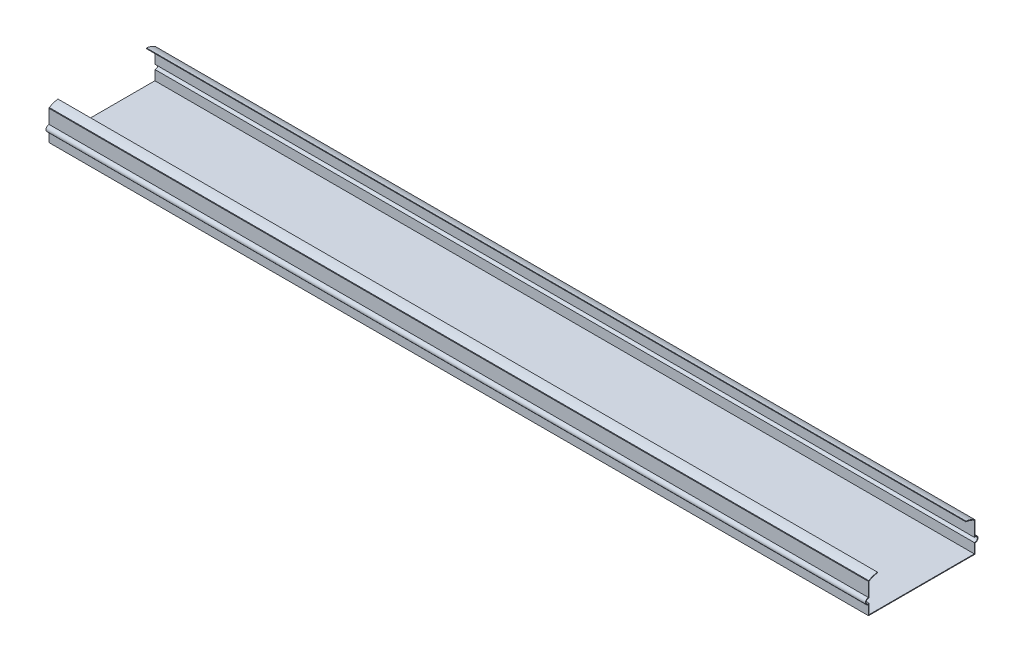
SolidWorks part; units mm, degrees
ref_plane "Front Plane" through (0, 0, 0) normal (0, 0, 1) x (1, 0, 0)
ref_plane "Top Plane" through (0, 0, 0) normal (0, 1, 0) x (1, 0, 0)
ref_plane "Right Plane" through (0, 0, 0) normal (1, 0, 0) x (0, 0, -1)
sketch "Sketch1" plane through (0, 0, 0) normal (0, 1, 0) x (1, 0, 0)
  line L0 (0, 16.5) -> (0, -16.5) construction
  line L1 (-133.0182, 16.5) -> (120.9818, 16.5)
  line L2 (-133.0182, 16.5) -> (-133.0182, -16.5)
  line L3 (-133.0182, -16.5) -> (120.9818, -16.5)
  line L4 (120.9818, 16.5) -> (120.9818, -16.5)
  dimension "D1" = 254
  dimension "D2" = 33
extrude "Boss-Extrude1" add sketch "Sketch1" along normal blind 0.2
sketch "Sketch2" plane through (0, 0.2, 0) normal (0, 1, 0) x (1, 0, 0)
  line L0 (120.9818, 16.5) -> (-133.0182, 16.5) construction
  line L1 (120.9818, 16.5) -> (-133.0182, 16.5)
ref_plane "Plane1" through (-133.0182, 0, 0) normal (1, 0, 0) x (0, 0, -1)
sketch "Sketch4" plane through (-133.0182, 0, 0) normal (1, 0, 0) x (0, 0, -1)
  line L0 (16.5, 0.2) -> (16.5, 3.0056)
  line L1 (16.5, 4.8842) -> (16.5, 9.2)
  line L2 (-16.5, 0.2) -> (16.5, 0.2) construction
  line L3 (16.2968, 0.2) -> (16.2968, 3.2374)
  line L4 (16.2968, 4.6524) -> (16.2968, 9.2)
  line L5 (16.2968, 0.2) -> (16.5, 0.2)
  line L7 (13.7113, 10.2998) -> (13.6934, 10.0974)
  line L8 (16.4065, 9.371) -> (16.5, 9.2)
  arc A0 (16.5, 3.0056) -> (16.5, 4.8842) centre (16.5, 3.9449) ccw
  arc A1 (16.2968, 3.2374) -> (16.2968, 4.6524) centre (16.5, 3.9449) ccw
  spline S0 degree 2 poles (16.2968, 9.2) (15.0897, 9.9741) (13.6934, 10.0974) knots 0 0 0 1 1 1
  spline S1 degree 1 poles (16.4065, 9.371) (13.7113, 10.2998) knots 0 0 1 1 construction
  spline S2 degree 3 poles (16.4065, 9.371) (15.6066, 9.884) (14.6578, 10.2162) (13.7113, 10.2998) knots 0 0 0 0 1 1 1 1
  dimension "D1" = 9.8974
  dimension "D2" = 0.2032
  dimension "D3" = 0.2032
extrude "Boss-Extrude2" add sketch "Sketch4" along normal blind 254
mirror "Mirror1" about plane through (0, 0, 0) normal (0, 0, 1) of "Boss-Extrude2"
